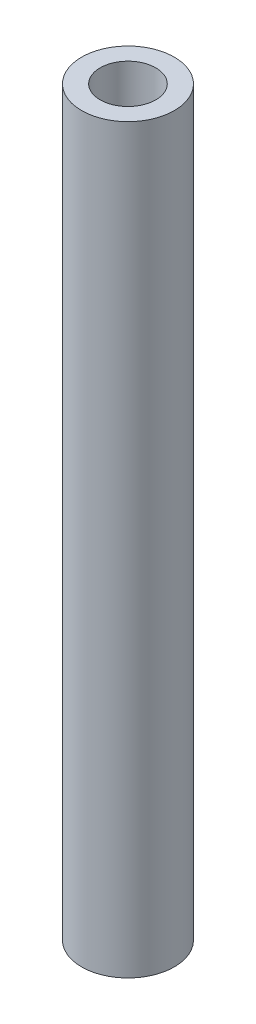
SolidWorks part; units mm, degrees
ref_plane "Front Plane" through (0, 0, 0) normal (0, 0, 1) x (1, 0, 0)
ref_plane "Top Plane" through (0, 0, 0) normal (0, 1, 0) x (1, 0, 0)
ref_plane "Right Plane" through (0, 0, 0) normal (1, 0, 0) x (0, 0, -1)
sketch "Sketch1" plane through (0, 0, 0) normal (0, 1, 0) x (1, 0, 0)
  circle A0 centre (0, 0) radius 1.5
  circle A1 centre (0, 0) radius 2.5
  dimension "D1" = 3
  dimension "D2" = 5
extrude "Boss-Extrude1" add sketch "Sketch1" along normal blind 40
